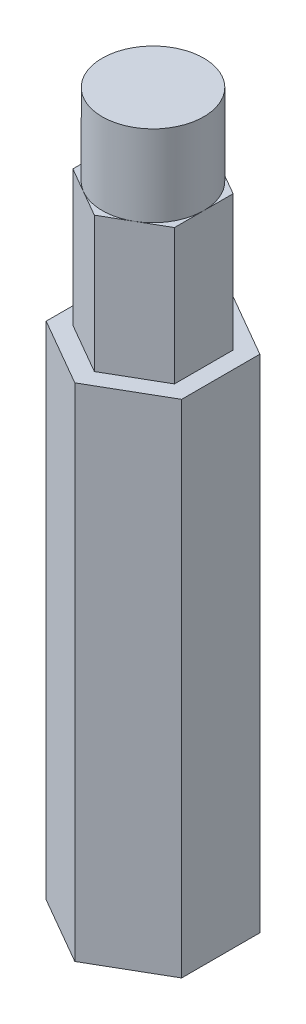
SolidWorks part; units mm, degrees
material "7075-T6 (SN)"
ref_plane "Front Plane" through (0, 0, 0) normal (0, 0, 1) x (1, 0, 0)
ref_plane "Top Plane" through (0, 0, 0) normal (0, 1, 0) x (1, 0, 0)
ref_plane "Right Plane" through (0, 0, 0) normal (1, 0, 0) x (0, 0, -1)
sketch "Sketch1" plane through (0, 0, 0) normal (0, 1, 0) x (1, 0, 0)
  line L1 (6.35, -3.6662) -> (6.35, 3.6662)
  line L2 (6.35, 3.6662) -> (0, 7.3323)
  line L3 (0, 7.3323) -> (-6.35, 3.6662)
  line L4 (-6.35, 3.6662) -> (-6.35, -3.6662)
  line L5 (-6.35, -3.6662) -> (0, -7.3323)
  line L6 (0, -7.3323) -> (6.35, -3.6662)
  circle A0 centre (0, 0) radius 6.35 construction
  dimension "D1" = 12.7
extrude "Boss-Extrude1" add sketch "Sketch1" along normal blind 59.69
sketch "Sketch2" plane through (0, 0, 0) normal (0, 1, 0) x (1, 0, 0)
  circle A0 centre (0, 0) radius 4.7625
  dimension "D1" = 9.525
extrude "Boss-Extrude2" add sketch "Sketch2" along normal blind 67.31
sketch "Sketch3" plane through (0, 59.69, 0) normal (0, 1, 0) x (1, 0, 0)
  line L0 (-6.35, -3.6662) -> (0, -7.3323) construction
  line L1 (4.7625, -2.7496) -> (4.7625, 2.7496)
  line L2 (4.7625, 2.7496) -> (0, 5.4993)
  line L3 (0, 5.4993) -> (-4.7625, 2.7496)
  line L4 (-4.7625, 2.7496) -> (-4.7625, -2.7496)
  line L5 (-4.7625, -2.7496) -> (0, -5.4993)
  line L6 (0, -5.4993) -> (4.7625, -2.7496)
  line L13 (0, -7.3323) -> (6.35, -3.6662)
  line L14 (6.35, -3.6662) -> (6.35, 3.6662)
  line L15 (6.35, 3.6662) -> (0, 7.3323)
  line L16 (0, 7.3323) -> (-6.35, 3.6662)
  line L17 (-6.35, 3.6662) -> (-6.35, -3.6662)
  line L18 (-6.35, -3.6662) -> (0, -7.3323)
  line L19 (0, -7.3323) -> (6.35, -3.6662)
  line L20 (6.35, -3.6662) -> (6.35, 3.6662)
  line L21 (6.35, 3.6662) -> (0, 7.3323)
  line L22 (0, 7.3323) -> (-6.35, 3.6662)
  line L23 (-6.35, 3.6662) -> (-6.35, -3.6662)
  line L24 (-6.35, -3.6662) -> (0, -7.3323)
  circle A0 centre (0, 0) radius 4.7625 construction
  dimension "D1" = 9.525
  dimension "D2" = 0
extrude "Cut-Extrude1" cut sketch "Sketch3" against normal blind 12.7
